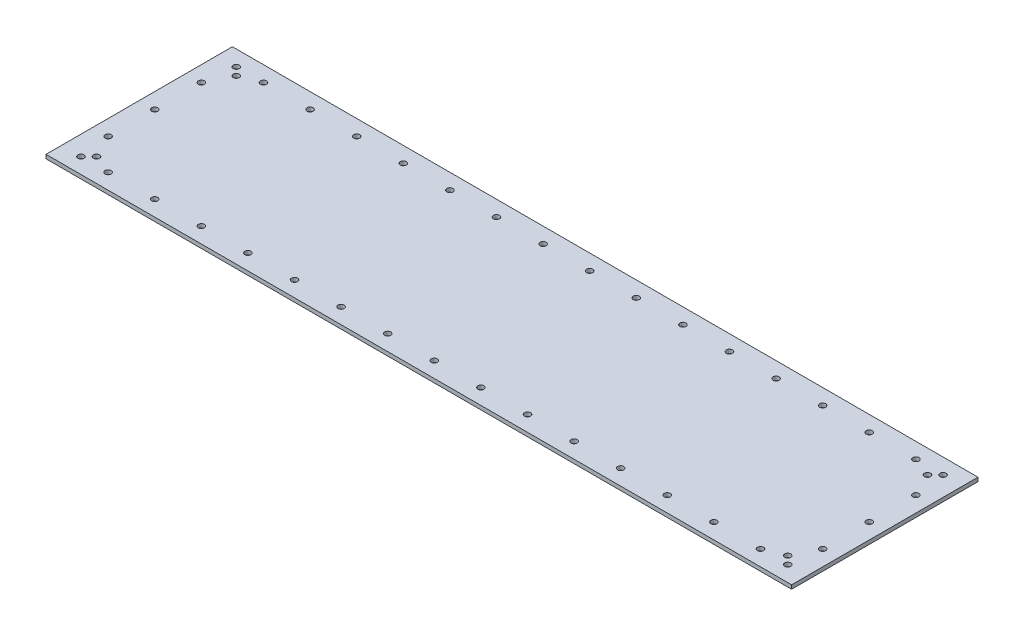
SolidWorks part; units mm, degrees
ref_plane "Front Plane" through (0, 0, 0) normal (0, 0, 1) x (1, 0, 0)
ref_plane "Top Plane" through (0, 0, 0) normal (0, 1, 0) x (1, 0, 0)
ref_plane "Right Plane" through (0, 0, 0) normal (1, 0, 0) x (0, 0, -1)
sketch "Sketch1" plane through (0, 0, 0) normal (0, 1, 0) x (1, 0, 0)
  line L1 (304.8, -76.2) -> (-304.8, -76.2)
  line L2 (304.8, -76.2) -> (304.8, 76.2)
  line L3 (304.8, 76.2) -> (-304.8, 76.2)
  line L4 (-304.8, -76.2) -> (-304.8, 76.2)
  line L5 (304.8, -76.2) -> (-304.8, 76.2) construction
  line L6 (304.8, 76.2) -> (-304.8, -76.2) construction
  point P0 (0, 0)
  dimension "D1" = 152.4
  dimension "D2" = 609.6
extrude "Boss-Extrude1" add sketch "Sketch1" along normal blind 3.175
sketch "Sketch2" plane through (0, 3.175, 0) normal (0, 1, 0) x (1, 0, 0)
  line L0 (-304.8, 76.2) -> (-304.8, -76.2) construction
  line L1 (304.8, 76.2) -> (-304.8, 76.2) construction
  line L2 (0, 76.2) -> (0, 0) construction
  line L3 (-292.1, 38.1) -> (-292.1, 0) construction
  line L4 (292.1, 38.1) -> (292.1, 0) construction
  line L5 (-304.8, 0) -> (0, 0) construction
  circle A0 centre (-288.925, 63.5) radius 2.5
  circle A1 centre (-282.575, 57.15) radius 2.5
  circle A2 centre (282.575, 57.15) radius 2.5
  circle A3 centre (288.925, 63.5) radius 2.5
  circle A4 centre (-266.7, 63.5) radius 2.5
  circle A5 centre (-228.6, 63.5) radius 2.5
  circle A6 centre (-190.5, 63.5) radius 2.5
  circle A7 centre (-152.4, 63.5) radius 2.5
  circle A8 centre (-114.3, 63.5) radius 2.5
  circle A9 centre (-76.2, 63.5) radius 2.5
  circle A10 centre (-38.1, 63.5) radius 2.5
  circle A11 centre (0, 63.5) radius 2.5
  circle A12 centre (38.1, 63.5) radius 2.5
  circle A13 centre (76.2, 63.5) radius 2.5
  circle A14 centre (114.3, 63.5) radius 2.5
  circle A15 centre (-292.1, 38.1) radius 2.5
  circle A16 centre (-292.1, 0) radius 2.5
  circle A17 centre (-292.1, -38.1) radius 2.5
  circle A26 centre (292.1, -38.1) radius 2.5
  circle A27 centre (292.1, 0) radius 2.5
  circle A28 centre (292.1, 38.1) radius 2.5
  circle A29 centre (152.4, 63.5) radius 2.5
  circle A30 centre (190.5, 63.5) radius 2.5
  circle A31 centre (228.6, 63.5) radius 2.5
  circle A32 centre (266.7, 63.5) radius 2.5
  circle A33 centre (266.7, -63.5) radius 2.5
  circle A34 centre (228.6, -63.5) radius 2.5
  circle A35 centre (190.5, -63.5) radius 2.5
  circle A36 centre (152.4, -63.5) radius 2.5
  circle A37 centre (114.3, -63.5) radius 2.5
  circle A38 centre (76.2, -63.5) radius 2.5
  circle A39 centre (38.1, -63.5) radius 2.5
  circle A40 centre (0, -63.5) radius 2.5
  circle A41 centre (-38.1, -63.5) radius 2.5
  circle A42 centre (-76.2, -63.5) radius 2.5
  circle A43 centre (-114.3, -63.5) radius 2.5
  circle A44 centre (-152.4, -63.5) radius 2.5
  circle A45 centre (-190.5, -63.5) radius 2.5
  circle A46 centre (-228.6, -63.5) radius 2.5
  circle A47 centre (-266.7, -63.5) radius 2.5
  circle A48 centre (288.925, -63.5) radius 2.5
  circle A49 centre (282.575, -57.15) radius 2.5
  circle A50 centre (-282.575, -57.15) radius 2.5
  circle A51 centre (-288.925, -63.5) radius 2.5
  dimension "D1" = 5
  dimension "D2" = 15.875
  dimension "D3" = 12.7
  dimension "D4" = 19.05
  dimension "D5" = 22.225
  dimension "D7" = 12.7
  dimension "D8" = 38.1
  dimension "D9" = 38.1
  dimension "D10" = 38.1
  dimension "D11" = 12.7
  dimension "D13" = 38.1
  dimension "D6" = 15
  dimension "D12" = 3
extrude "Cut-Extrude1" cut sketch "Sketch2" against normal blind 3.175
